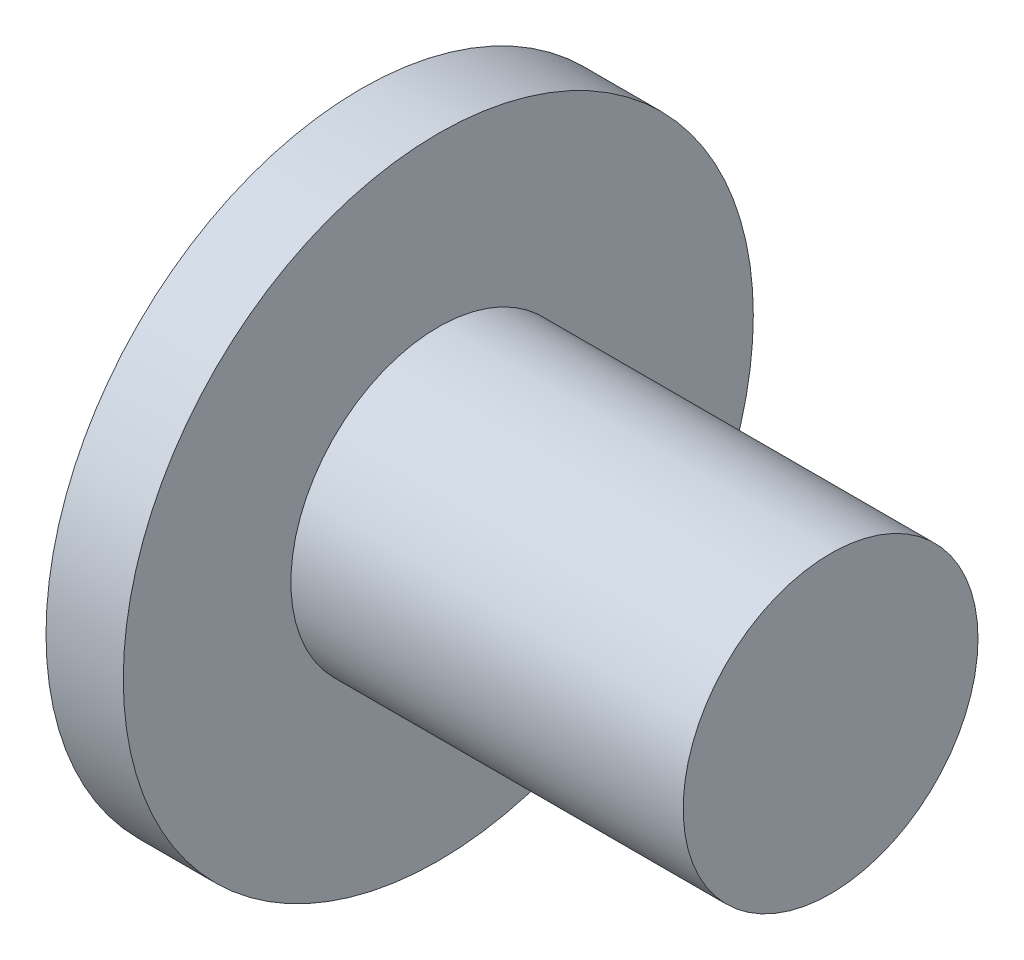
SolidWorks part; units mm, degrees
ref_plane "Front Plane" through (0, 0, 0) normal (0, 0, 1) x (1, 0, 0)
ref_plane "Top Plane" through (0, 0, 0) normal (0, 1, 0) x (1, 0, 0)
ref_plane "Right Plane" through (0, 0, 0) normal (1, 0, 0) x (0, 0, -1)
sketch "Sketch1" plane through (0, 0, 0) normal (1, 0, 0) x (0, 0, -1)
  circle A0 centre (0, 0) radius 6.731
  dimension "D1" = 13.462
extrude "Boss-Extrude1" add sketch "Sketch1" along normal blind 1.651
sketch "Sketch2" plane through (1.651, 0, 0) normal (1, 0, 0) x (0, 0, -1)
  circle A0 centre (0, 0) radius 3.1496
  dimension "D1" = 6.2992
extrude "Boss-Extrude2" add sketch "Sketch2" along normal blind 8.382
sketch "Sketch3" plane through (0, 0, 0) normal (-1, 0, 0) x (0, 0, 1)
  point P0 (0, 0)
